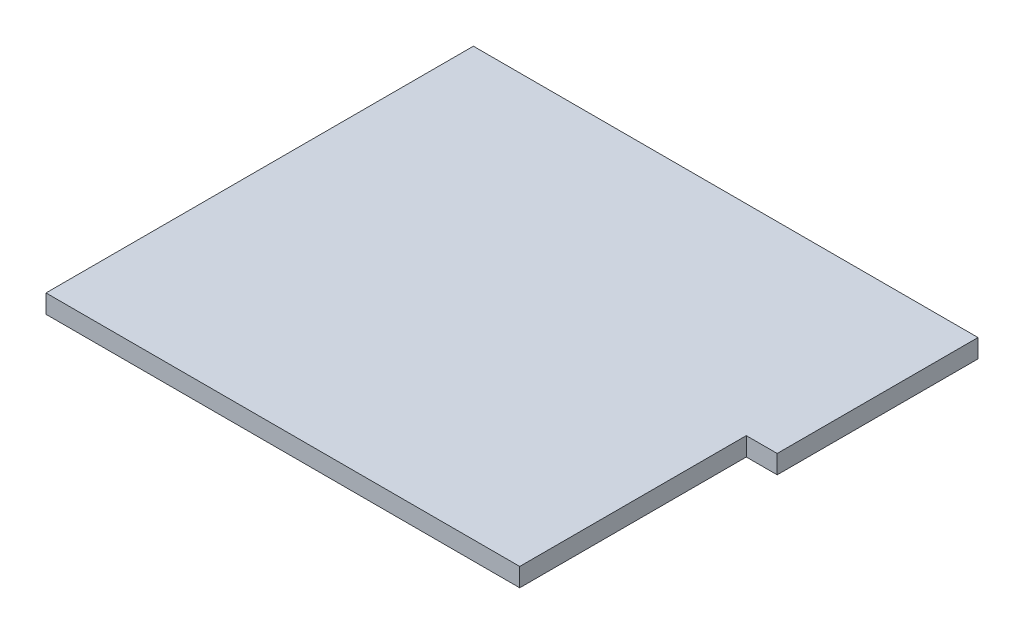
SolidWorks part; units mm, degrees
material "Zoltek Panex 33"
ref_plane "Płaszczyzna przednia" through (0, 0, 0) normal (0, 0, 1) x (1, 0, 0)
ref_plane "Płaszczyzna górna" through (0, 0, 0) normal (0, 1, 0) x (1, 0, 0)
ref_plane "Płaszczyzna prawa" through (0, 0, 0) normal (1, 0, 0) x (0, 0, -1)
sketch "Szkic1" plane through (0, 0, 0) normal (0, 1, 0) x (1, 0, 0)
  line L0 (0, 0) -> (454, 0)
  line L1 (454, 0) -> (454, 220)
  line L2 (454, 220) -> (484, 220)
  line L3 (484, 220) -> (484, 409)
  line L4 (484, 409) -> (0, 409)
  line L5 (0, 409) -> (0, 0)
  dimension "D1" = 409
  dimension "D2" = 484
  dimension "D3" = 30
  dimension "D4" = 189
extrude "Dodanie-wyciągnięcie1" add sketch "Szkic1" against normal blind 15
shell "Skorupa1" thickness 3
